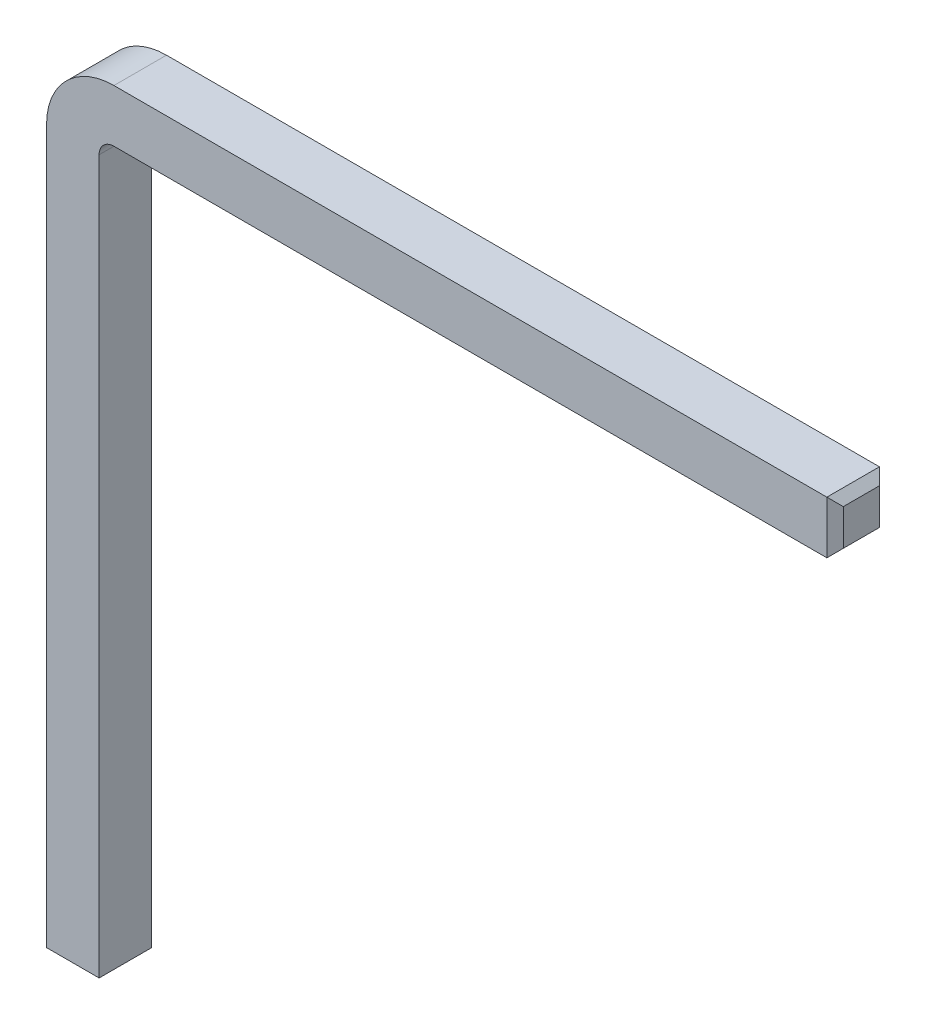
SolidWorks part; units mm, degrees
ref_plane "Front" through (0, 0, 0) normal (0, 0, 1) x (1, 0, 0)
ref_plane "Top" through (0, 0, 0) normal (0, 1, 0) x (1, 0, 0)
ref_plane "Right" through (0, 0, 0) normal (1, 0, 0) x (0, 0, -1)
sketch "Эскиз1" plane through (0, 0, 0) normal (0, 1, 0) x (1, 0, 0)
  line L1 (-0.32, 0.32) -> (0.32, 0.32)
  line L2 (-0.32, 0.32) -> (-0.32, -0.32)
  line L3 (-0.32, -0.32) -> (0.32, -0.32)
  line L4 (0.32, 0.32) -> (0.32, -0.32)
  line L5 (-0.32, 0.32) -> (0.32, -0.32) construction
  line L6 (-0.32, -0.32) -> (0.32, 0.32) construction
  point P0 (0, 0)
  dimension "D1" = 0.64
  dimension "D2" = 0.64
sketch "Эскиз2" plane through (0, 0, 0) normal (0, 0, 1) x (1, 0, 0)
  line L0 (0, 0) -> (0, 8.78)
  line L1 (0.5, 9.28) -> (9.28, 9.28)
  arc A0 (0, 8.78) -> (0.5, 9.28) centre (0.5, 8.78) cw
  point P6 (0, 9.28)
  dimension "D3" = 0.5
  dimension "D1" = 9.28
  dimension "D2" = 9.28
sweep "По траектории1" add profiles "Эскиз1" path "Эскиз2"
chamfer "Фаска1" distance 0.1 angle 45 8 edges at (0, 0, 0.32) (0, 0, -0.32) (-0.32, 0, 0) (0.32, 0, 0) (9.28, 9.28, -0.32) (9.28, 9.28, 0.32) (9.28, 9.6, 0) (9.28, 8.96, 0)
equation "\"D2@Эскиз1\"=\"D1@Эскиз1\""
